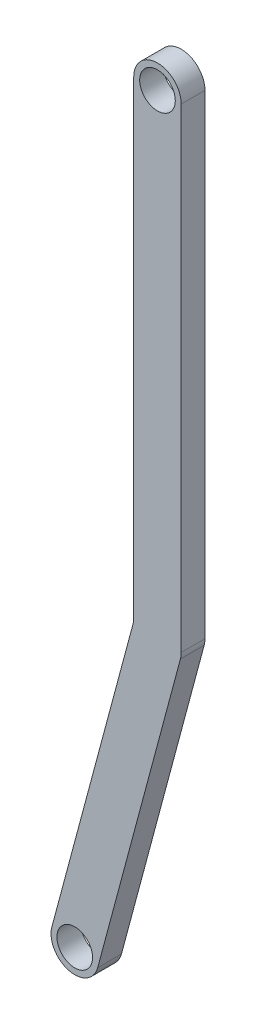
SolidWorks part; units mm, degrees
ref_plane "Front Plane" through (0, 0, 0) normal (0, 0, 1) x (1, 0, 0)
ref_plane "Top Plane" through (0, 0, 0) normal (0, 1, 0) x (1, 0, 0)
ref_plane "Right Plane" through (0, 0, 0) normal (1, 0, 0) x (0, 0, -1)
sketch "Sketch1" plane through (0, 0, 0) normal (0, 0, 1) x (1, 0, 0)
  line L0 (0, 0) -> (0, -20) construction
  line L1 (1, 0) -> (1, -20)
  line L2 (-1, 0) -> (-1, -20)
  line L3 (0, -20) -> (-3.4833, -33) construction
  line L4 (0.9659, -20.2588) -> (-2.5174, -33.2588)
  line L5 (-0.9659, -19.7412) -> (-4.4493, -32.7412)
  arc A0 (1, 0) -> (-1, 0) centre (0, 0) ccw
  arc A1 (-1, -20) -> (1, -20) centre (0, -20) ccw
  arc A2 (0.9659, -20.2588) -> (-0.9659, -19.7412) centre (0, -20) ccw
  arc A3 (-4.4493, -32.7412) -> (-2.5174, -33.2588) centre (-3.4833, -33) ccw
  circle A4 centre (-21.9232, -192.0319) radius 0.75
  circle A5 centre (0, 0) radius 0.75
  circle A6 centre (-3.4833, -33) radius 0.75
  point P2 (0, -10)
  point P7 (-1.7417, -26.5)
  dimension "D2" = 1
  dimension "D3" = 1.5
  dimension "D4" = 1.5
  dimension "D7" = 1.5
  dimension "D1" = 165
  dimension "D5" = 20
  dimension "D6" = 33
extrude "Boss-Extrude1" add sketch "Sketch1" along normal blind 1 contours L5 A3 L4 A1 L2 A6 | A1 A2 L5 L2 | A2 L1 A0 L2 L5 A5
